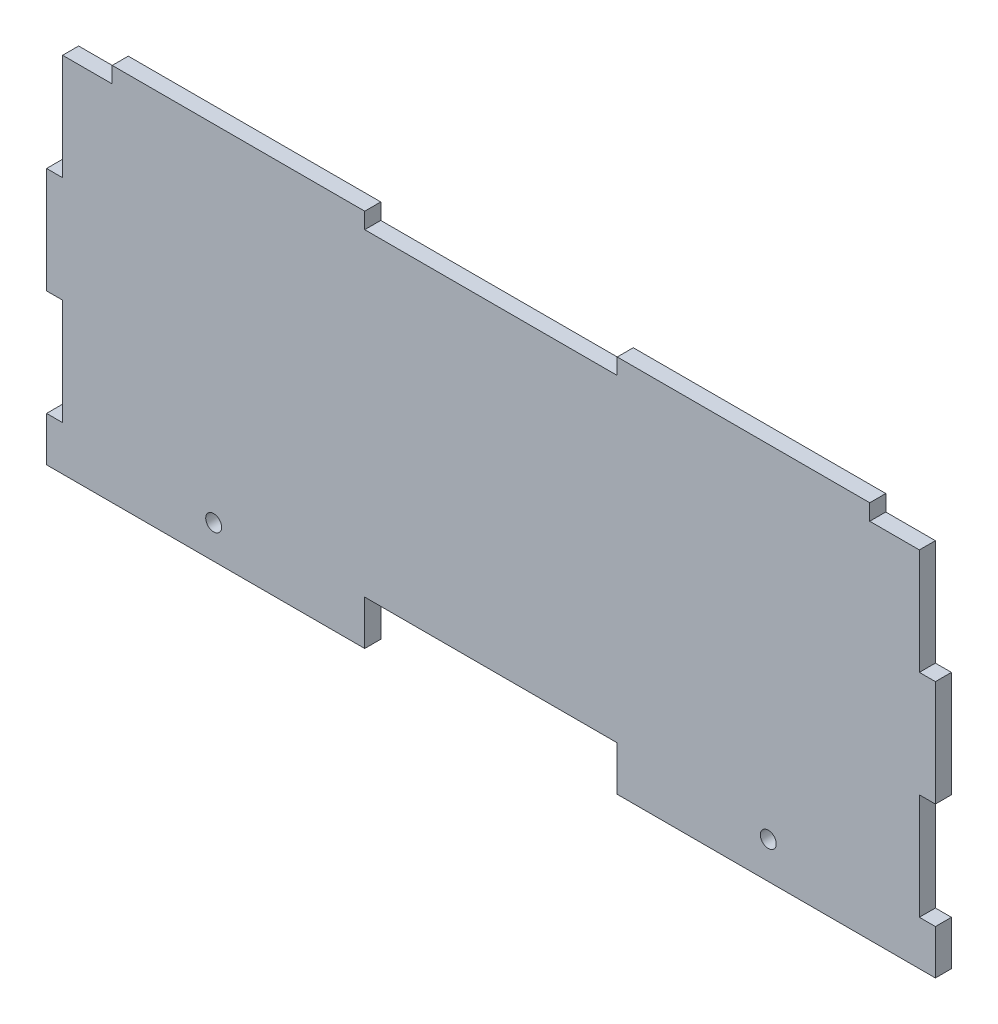
SolidWorks part; units mm, degrees
ref_plane "Front Plane" through (0, 0, 0) normal (0, 0, 1) x (1, 0, 0)
ref_plane "Top Plane" through (0, 0, 0) normal (0, 1, 0) x (1, 0, 0)
ref_plane "Right Plane" through (0, 0, 0) normal (1, 0, 0) x (0, 0, -1)
sketch "Sketch1" plane through (0, 0, 0) normal (0, 0, 1) x (1, 0, 0)
  line L0 (0, 71.825) -> (176, 71.825) construction
  line L1 (176, 75) -> (0, 75)
  line L2 (176, 75) -> (176, 0)
  line L3 (-0.0877, 0) -> (176, 0)
  line L4 (0, 75) -> (0, 0)
  line L5 (13, 75) -> (13, 71.825)
  line L6 (163, 75) -> (163, 71.825)
  line L7 (63, 75) -> (63, 71.825)
  line L8 (63, 71.825) -> (113, 71.825)
  line L9 (113, 71.825) -> (113, 75)
  line L10 (0, 8.825) -> (176, 8.825) construction
  line L11 (176, 8.825) -> (113, 8.825) construction
  line L12 (63, 8.825) -> (63, 0)
  line L13 (0, 8.825) -> (63, 8.825) construction
  line L14 (113, 8.825) -> (113, 0)
  line L15 (113, 8.825) -> (63, 8.825)
  line L16 (176, 8.825) -> (172.825, 8.825)
  line L17 (172.825, 75) -> (172.825, 0) construction
  line L18 (3.175, 71.825) -> (13, 71.825)
  line L19 (172.825, 71.825) -> (163, 71.825)
  line L20 (3.175, 75) -> (3.175, 0) construction
  line L21 (0, 50.825) -> (3.175, 50.825)
  line L22 (0, 29.825) -> (3.175, 29.825)
  line L23 (3.175, 50.825) -> (3.175, 71.825)
  line L24 (172.825, 29.825) -> (176, 29.825)
  line L25 (172.825, 50.825) -> (176, 50.825)
  line L26 (172.825, 50.825) -> (172.825, 71.825)
  line L27 (113, 5.65) -> (172.825, 5.65) construction
  line L28 (0, 0) -> (-0.0877, 0) construction
  line L29 (33.0875, 4.4125) -> (33.0875, 8.825) construction
  line L30 (172.825, 7.2375) -> (113, 7.2375) construction
  line L31 (3.175, 6.6187) -> (63, 6.6188) construction
  line L32 (3.175, 29.825) -> (3.175, 8.825)
  line L33 (142.9125, 8.825) -> (142.9125, 5.65) construction
  line L34 (3.175, 8.825) -> (0, 8.825)
  line L35 (172.825, 29.825) -> (172.825, 8.825)
  line L36 (63, 4.4125) -> (3.175, 4.4125) construction
  circle A0 centre (33.0875, 6.6187) radius 1.575
  circle A1 centre (142.9125, 7.2375) radius 3 construction
  circle A2 centre (142.9125, 7.2375) radius 1.575
  circle A3 centre (33.0875, 6.6187) radius 3 construction
  point P0 (0, 0)
  point P18 (31.5, 8.825)
  point P19 (0, 0)
  point P23 (63, 4.4125)
  point P25 (172.825, 7.2375)
  point P45 (142.9125, 7.2375)
  point P54 (0, 0)
  point P59 (172.825, 5.65)
  point P60 (0, 0)
  point P61 (142.9125, 5.65)
  point P62 (142.9125, 7.2375)
  point P63 (0, 0)
  point P66 (0, 5.65)
  point P67 (0, 0)
  point P68 (0, 0)
  point P69 (0, 7.2375)
  point P70 (0, 0)
  point P71 (0, 0)
  point P72 (0, 5.65)
  point P73 (0, 0)
  point P74 (3.175, 5.65)
  point P75 (59.825, 5.65)
  point P76 (0, 0)
  point P77 (33.0875, 6.6187)
  point P80 (0, 0)
  point P81 (0, 7.2375)
  point P82 (0, 0)
  point P83 (3.175, 7.2375)
  point P84 (0, 0)
  point P85 (0, 0)
  point P86 (31.5, 8.825)
  point P87 (0, 0)
  point P88 (31.5, 29.0123)
  point P89 (59.825, 16.6851)
  point P90 (0, 0)
  point P91 (0, 0)
  point P92 (59.825, 15.9331)
  point P93 (0, 0)
  point P94 (59.825, 5.65)
  point P95 (59.825, 3.3819)
  point P96 (31.5, 5.65)
  point P97 (0, 0)
  point P98 (0, 0)
  point P99 (63, 17.4844)
  point P100 (63, 21.0259)
  point P101 (0, 0)
  point P102 (33.0875, 4.4125)
  point P103 (0, 0)
  point P104 (0, 0)
  dimension "D14" = 3.15
  dimension "D15" = 3.15
  dimension "D16" = 6
  dimension "D17" = 6
  dimension "D1" = 75
  dimension "D2" = 176
  dimension "D3" = 13
  dimension "D4" = 13
  dimension "D5" = 3.175
  dimension "D6" = 50
  dimension "D7" = 50
  dimension "D8" = 50
  dimension "D9" = 21
  dimension "D10" = 3.175
  dimension "D11" = 21
  dimension "D12" = 21
  dimension "D13" = 3.175
  dimension "D18" = 3.175
extrude "Boss-Extrude1" add sketch "Sketch1" along normal mid plane 3.175
